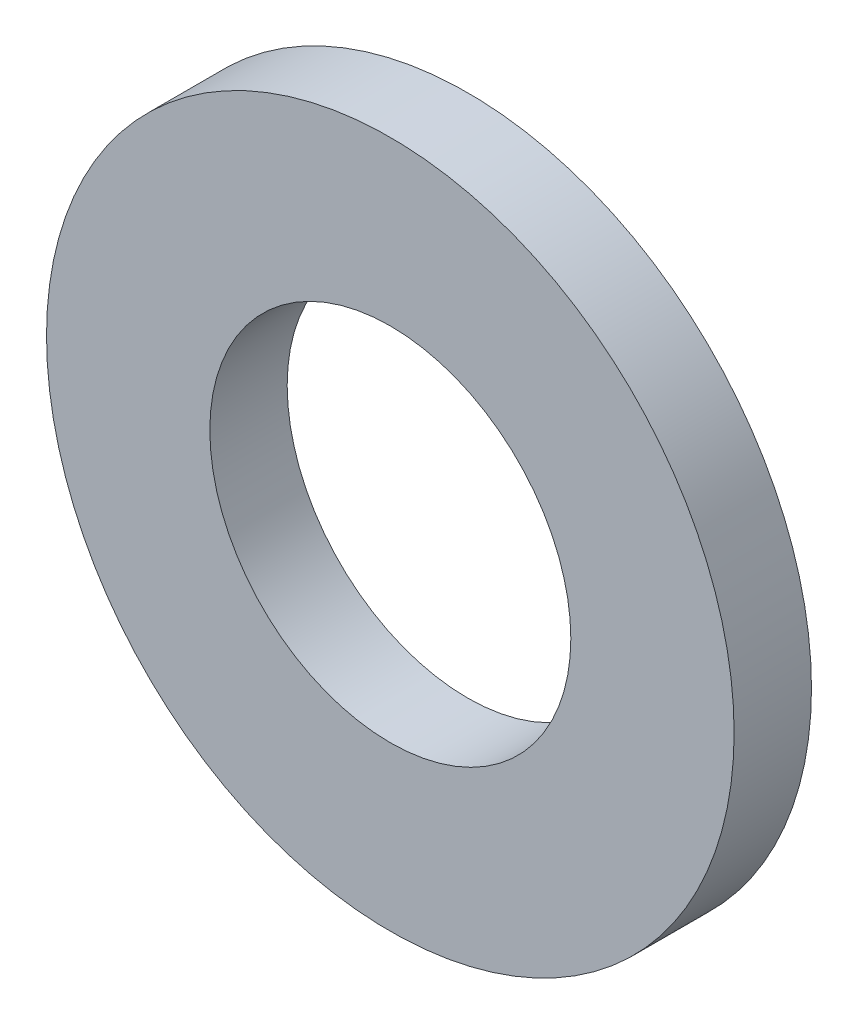
SolidWorks part; units mm, degrees
ref_plane "Front Plane" through (0, 0, 0) normal (0, 0, 1) x (1, 0, 0)
ref_plane "Top Plane" through (0, 0, 0) normal (0, 1, 0) x (1, 0, 0)
ref_plane "Right Plane" through (0, 0, 0) normal (1, 0, 0) x (0, 0, -1)
sketch "Sketch1" plane through (0, 0, 0) normal (0, 0, 1) x (1, 0, 0)
  circle A0 centre (0, 0) radius 8
  circle A1 centre (0, 0) radius 4.2
  dimension "OD" = 16
  dimension "ID1" = 8.4
extrude "Boss-Extrude1" add sketch "Sketch1" along normal blind 1.8
